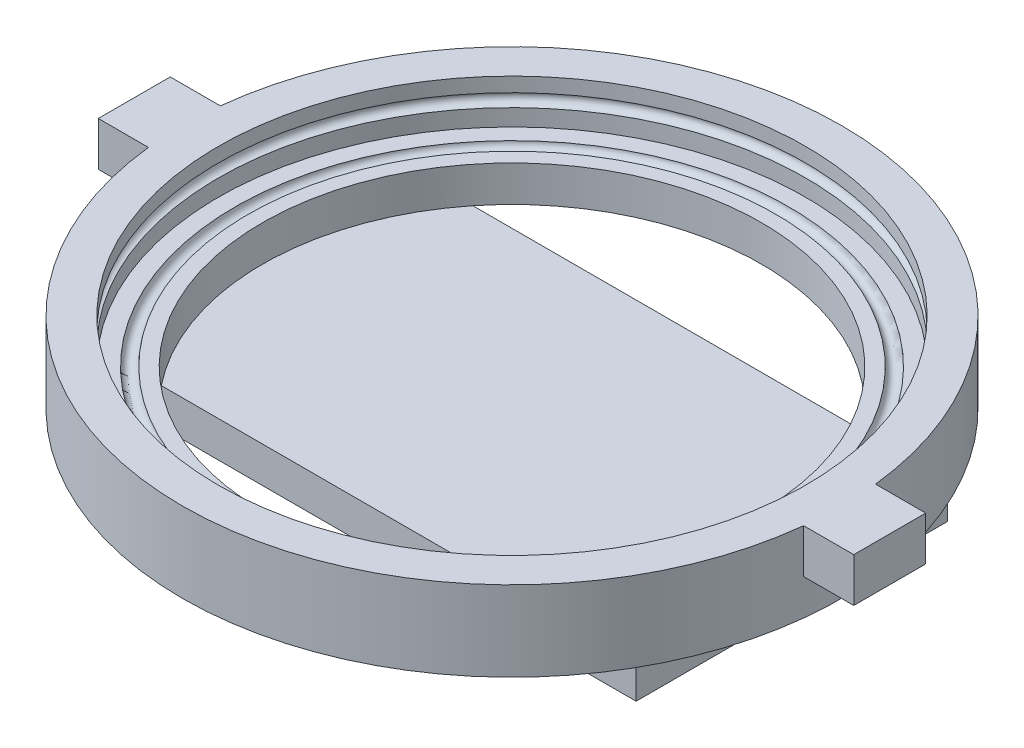
SolidWorks part; units mm, degrees
ref_plane "Front Plane" through (0, 0, 0) normal (0, 0, 1) x (1, 0, 0)
ref_plane "Top Plane" through (0, 0, 0) normal (0, 1, 0) x (1, 0, 0)
ref_plane "Right Plane" through (0, 0, 0) normal (1, 0, 0) x (0, 0, -1)
sketch "Sketch1" plane through (0, 0, 0) normal (0, 0, 1) x (1, 0, 0)
  line L0 (0, 0) -> (0, -25.4) construction
  line L1 (102.8192, -10.668) -> (102.8192, -15.748) construction
  line L2 (102.8192, -20.32) -> (102.8192, -25.4) construction
  line L3 (102.8192, -25.4) -> (97.7392, -25.4) construction
  line L4 (93.1672, -25.4) -> (88.0872, -25.4) construction
  line L5 (103.6447, -10.668) -> (103.6447, -15.748)
  line L6 (103.6447, -20.32) -> (103.6447, -26.2255)
  line L7 (103.6447, -26.2255) -> (97.7392, -26.2255)
  line L8 (93.1672, -26.2255) -> (88.0872, -26.2255)
  line L9 (103.6447, -10.668) -> (116.3447, -10.668)
  line L10 (116.3447, -10.668) -> (116.3447, -38.9255)
  line L11 (116.3447, -38.9255) -> (88.0872, -38.9255)
  line L12 (88.0872, -38.9255) -> (88.0872, -26.2255)
  arc A0 (102.8192, -15.748) -> (102.8192, -20.32) centre (102.8192, -18.034) ccw construction
  arc A1 (97.7392, -25.4) -> (93.1672, -25.4) centre (95.4532, -25.4) ccw construction
  arc A2 (103.6447, -15.748) -> (103.6447, -20.32) centre (103.6447, -18.034) cw
  arc A3 (97.7392, -26.2255) -> (93.1672, -26.2255) centre (95.4532, -26.2255) cw
  dimension "D2" = 2.286
  dimension "D1" = 25.4
  dimension "D3" = 5.08
  dimension "D4" = 25.4
  dimension "D5" = 102.8192
  dimension "D6" = 0.8255
  dimension "D7" = 0.8255
  dimension "D8" = 5.9055
  dimension "D9" = 5.9055
  dimension "D10" = 5.08
  dimension "D11" = 5.08
  dimension "D12" = 12.7
  dimension "D13" = 12.7
revolve "Revolve1" add sketch "Sketch1" angle 360 about L0
sketch "Sketch2" plane through (0, -38.9255, 0) normal (0, -1, 0) x (1, 0, 0)
  line L1 (-98.806, 54.991) -> (98.806, 54.991)
  line L2 (-98.806, 54.991) -> (-98.806, -54.991)
  line L3 (-98.806, -54.991) -> (98.806, -54.991)
  line L4 (98.806, 54.991) -> (98.806, -54.991)
  dimension "D1" = 109.982
  dimension "D2" = 197.612
  dimension "D3" = 98.806
  dimension "D4" = 54.991
extrude "Boss-Extrude1" add sketch "Sketch2" along normal blind 12.7
sketch "Sketch3" plane through (0, -10.668, 0) normal (0, 1, 0) x (1, 0, 0)
  line L0 (133.35, 12.7) -> (133.35, -12.7)
  line L1 (133.35, -12.7) -> (114.3, -12.7)
  line L2 (133.35, 12.7) -> (114.3, 12.7)
  line L3 (-133.35, 12.7) -> (-133.35, -12.7)
  line L4 (-133.35, -12.7) -> (-114.3, -12.7)
  line L5 (-133.35, 12.7) -> (-114.3, 12.7)
  line L6 (-114.3, 12.7) -> (-114.3, -12.7)
  line L7 (114.3, 12.7) -> (114.3, -12.7)
  dimension "D3" = 114.3
  dimension "D1" = 12.7
  dimension "D2" = 25.4
  dimension "D4" = 133.35
  dimension "D5" = 25.4
  dimension "D6" = 12.7
  dimension "D7" = 114.3
  dimension "D8" = 133.35
extrude "Boss-Extrude2" add sketch "Sketch3" against normal up to surface (15.5575 mm away) up to face at (0, -26.2255, 97.7392)
